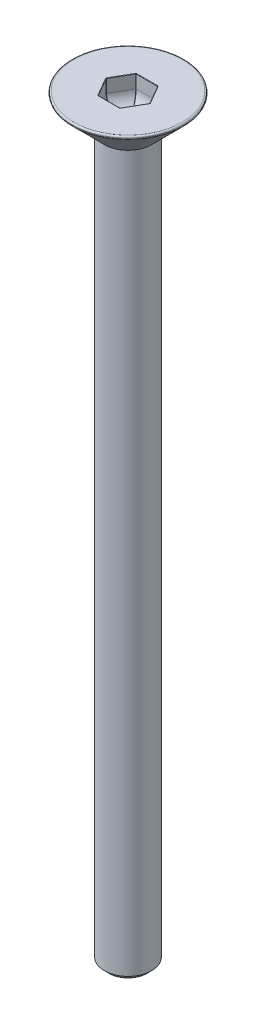
SolidWorks part; units mm, degrees
ref_plane "Front" through (0, 0, 0) normal (0, 0, 1) x (1, 0, 0)
ref_plane "Top" through (0, 0, 0) normal (0, 1, 0) x (1, 0, 0)
ref_plane "Right" through (0, 0, 0) normal (1, 0, 0) x (0, 0, -1)
sketch "Sketch8" plane through (0, 0, 0) normal (0, 0, 1) x (1, 0, 0)
  line L1 (0, 0) -> (1.25, 0)
  line L2 (0, 0) -> (0, -40)
  line L3 (0, -40) -> (1.25, -40)
  line L4 (1.25, 0) -> (1.25, -40)
  dimension "D1" = 40
revolve "Revolve1" add sketch "Sketch8" angle 360 about L2
chamfer "Chamfer1" distance 0.25 angle 45 1 edges at (-1.25, -40, 0)
sketch "Sketch9" plane through (0, 0, 0) normal (0, 1, 0) x (1, 0, 0)
  circle A0 centre (0, 0) radius 1.5
thread "Thread2" pitch 0.5 start angle 0, offset 0, length 15, pitch 0.5, diameter 3
ref_plane "Plane2" through (-1.5, 0, 0) normal (0, 0, -1) x (1, 0, 0)
sketch "Thread Profile2" plane through (-1.5, 0, 0) normal (0, 0, -1) x (1, 0, 0)
  line L0 (0, 0) -> (0, 0.5) construction
  line L11 (0, 0.4375) -> (0, 0)
  line L12 (0, 0) -> (0.2706, 0.1563)
  line L13 (0.2706, 0.1563) -> (0.2706, 0.2813)
  line L15 (0.2706, 0.2813) -> (0, 0.4375)
  line L17 (0.2706, 0.2188) -> (0, 0.2188) construction
  point P3 (0, 0)
  dimension "Pitch" = 0.5
  dimension "Profile_Angle" = 60
  dimension "Profile_Land" = 0.125
  dimension "Profile_Height" = 0.2706
sketch "Sketch13" plane through (0, 0, 0) normal (0, 0, 1) x (1, 0, 0)
  line L0 (0, 0) -> (3.1, 0)
  line L1 (0, 0) -> (0, -3.1)
  line L2 (0, -3.1) -> (3.1, 0)
  line L3 (1.55, 0) -> (1.55, -1.55) construction
revolve "Revolve2" add sketch "Sketch13" angle 360 about L1
chamfer "Chamfer2" distance 0.2 angle 45 1 edges at (-3.1, 0, 0)
fillet "Fillet1" radius 0.08 2 edges at (2.9586, 0, 0) (2.9586, -0.1414, 0)
sketch "Sketch14" plane through (0, 0, 0) normal (0, 1, 0) x (1, 0, 0)
  line L1 (1.1547, 0) -> (0.5774, 1)
  line L2 (0.5774, 1) -> (-0.5774, 1)
  line L3 (-0.5774, 1) -> (-1.1547, 0)
  line L4 (-1.1547, 0) -> (-0.5774, -1)
  line L5 (-0.5774, -1) -> (0.5774, -1)
  line L6 (0.5774, -1) -> (1.1547, 0)
  circle A0 centre (0, 0) radius 1 construction
extrude "Cut-Extrude1" cut sketch "Sketch14" against normal blind 1.5
fillet "Fillet2" radius 0.8 6 edges at (0, -1.5, 1) (-0.866, -1.5, 0.5) (-0.866, -1.5, -0.5) (0, -1.5, -1) (0.866, -1.5, -0.5) (0.866, -1.5, 0.5)
fillet "Fillet5" radius 0.02 18 edges at (0, 0, -1) (-0.866, 0, -0.5) (-0.866, 0, 0.5) (0, 0, 1) (0.866, 0, 0.5) (0.866, 0, -0.5) (-0.8841, -1.2657, 0) (-0.4421, -1.2657, 0.7657) (0.4421, -1.2657, 0.7657) (0.8841, -1.2657, 0) (0.4421, -1.2657, -0.7657) (-0.4421, -1.2657, -0.7657) (-1.1547, -0.35, 0) (-0.5774, -0.35, 1) (0.5774, -0.35, 1) (1.1547, -0.35, 0) (0.5774, -0.35, -1) (-0.5774, -0.35, -1)
equation "\"length\"= 40"
equation "\"D1@Sketch8\"=\"length\""
